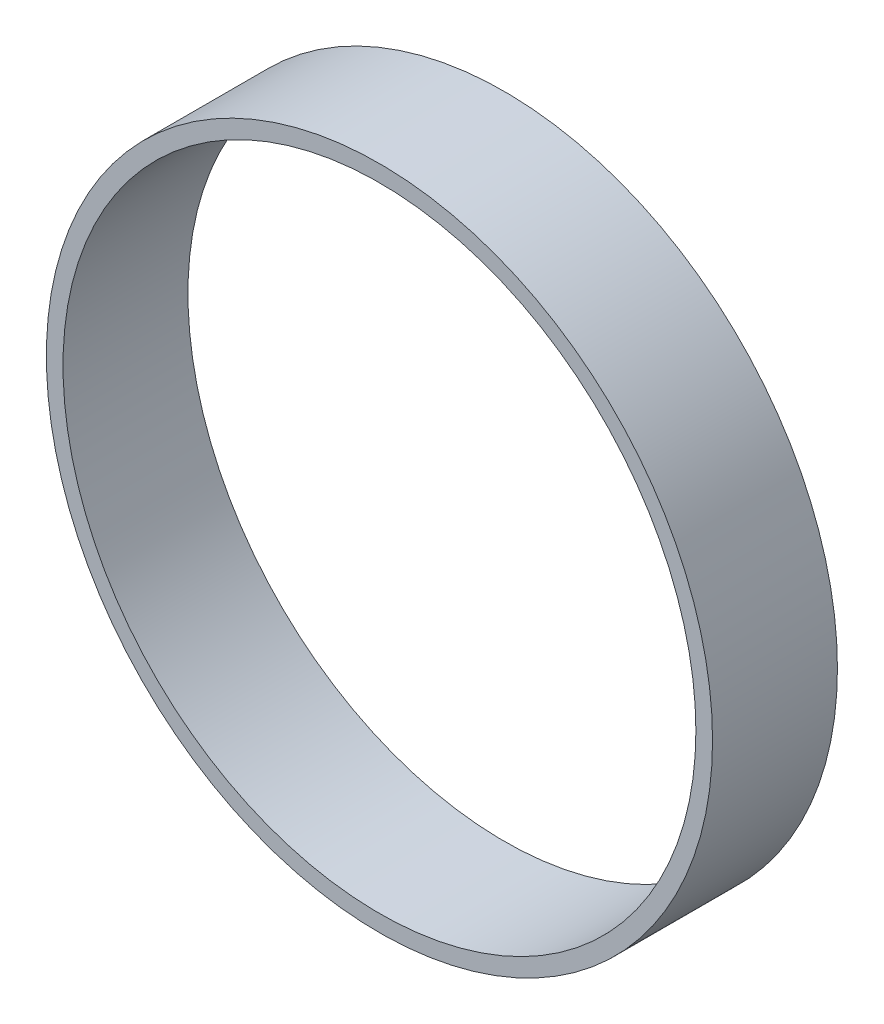
SolidWorks part; units mm, degrees
ref_plane "Front Plane" through (0, 0, 0) normal (0, 0, 1) x (1, 0, 0)
ref_plane "Top Plane" through (0, 0, 0) normal (0, 1, 0) x (1, 0, 0)
ref_plane "Right Plane" through (0, 0, 0) normal (1, 0, 0) x (0, 0, -1)
sketch "Sketch2" plane through (0, 0, 0) normal (0, 0, 1) x (1, 0, 0)
  line L5 (-50000, 50000) -> (50000, -50000) construction
  line L6 (-50000, -50000) -> (50000, 50000) construction
  circle A0 centre (0, 0) radius 40000
  circle A1 centre (0, 0) radius 38000
  point P0 (0, 0)
extrude "Boss-Extrude2" add sketch "Sketch2" along normal blind 15000
